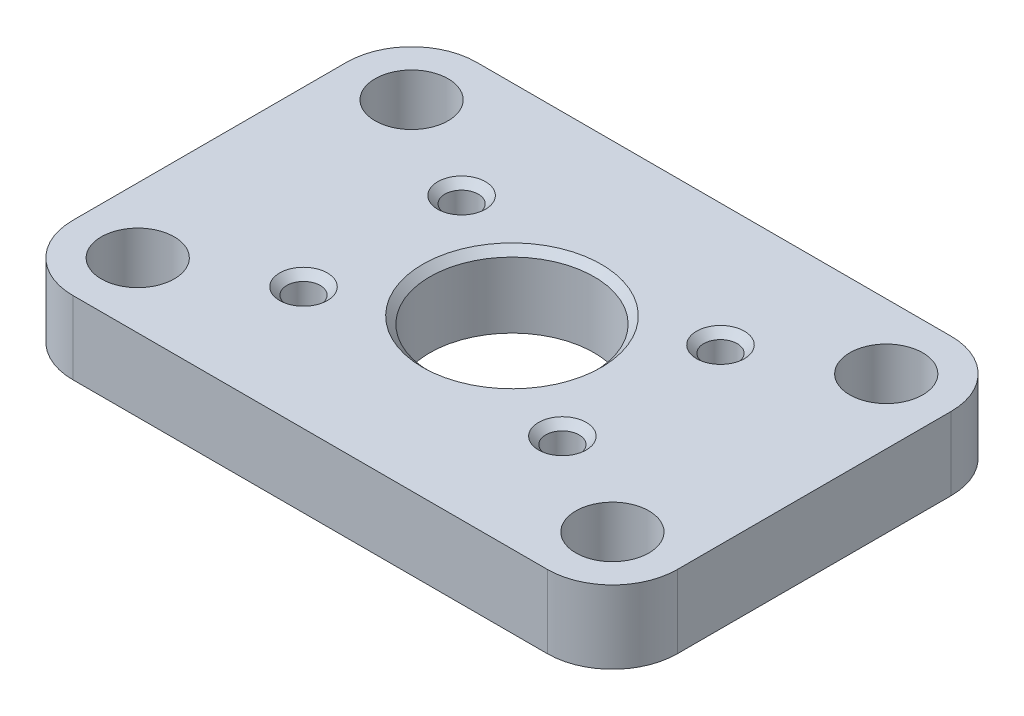
SolidWorks part; units mm, degrees
ref_plane "Front Plane" through (0, 0, 0) normal (0, 0, 1) x (1, 0, 0)
ref_plane "Top Plane" through (0, 0, 0) normal (0, 1, 0) x (1, 0, 0)
ref_plane "Right Plane" through (0, 0, 0) normal (1, 0, 0) x (0, 0, -1)
sketch "Sketch1" plane through (0, 0, 0) normal (0, 1, 0) x (1, 0, 0)
  line L1 (-16.51, -14.0462) -> (16.51, -14.0462)
  line L2 (-21.0312, -9.525) -> (-21.0312, 9.525)
  line L3 (-16.51, 14.0462) -> (16.51, 14.0462)
  line L4 (21.0312, -9.525) -> (21.0312, 9.525)
  line L5 (-21.0312, -14.0462) -> (21.0312, 14.0462) construction
  line L6 (-21.0312, 14.0462) -> (21.0312, -14.0462) construction
  arc A0 (16.51, -14.0462) -> (21.0312, -9.525) centre (16.51, -9.525) ccw
  arc A1 (16.51, 14.0462) -> (21.0312, 9.525) centre (16.51, 9.525) cw
  arc A2 (-16.51, -14.0462) -> (-21.0312, -9.525) centre (-16.51, -9.525) cw
  arc A3 (-21.0312, 9.525) -> (-16.51, 14.0462) centre (-16.51, 9.525) cw
  circle A4 centre (-16.51, 9.525) radius 2.54
  circle A5 centre (-16.51, -9.525) radius 2.54
  circle A6 centre (16.51, -9.525) radius 2.54
  circle A7 centre (16.51, 9.525) radius 2.54
  point P0 (0, 0)
  dimension "D1" = 4.5212
  dimension "D4" = 5.08
  dimension "D2" = 33.02
  dimension "D3" = 19.05
extrude "Boss-Extrude1" add sketch "Sketch1" along normal blind 5.08
sketch "Sketch3" plane through (0, 5.08, 0) normal (0, 1, 0) x (1, 0, 0)
  line L1 (-9.0043, -5.4991) -> (9.0043, -5.4991) construction
  line L2 (-9.0043, -5.4991) -> (-9.0043, 5.4991) construction
  line L3 (-9.0043, 5.4991) -> (9.0043, 5.4991) construction
  line L4 (9.0043, -5.4991) -> (9.0043, 5.4991) construction
  line L5 (-9.0043, -5.4991) -> (9.0043, 5.4991) construction
  line L6 (-9.0043, 5.4991) -> (9.0043, -5.4991) construction
  circle A0 centre (-9.0043, 5.4991) radius 1.162
  circle A1 centre (9.0043, 5.4991) radius 1.162
  circle A2 centre (9.0043, -5.4991) radius 1.162
  circle A3 centre (-9.0043, -5.4991) radius 1.162
  circle A4 centre (0, 0) radius 5.715
  point P0 (0, 0)
  dimension "D1" = 2.3241
  dimension "D4" = 11.43
  dimension "D2" = 10.9982
  dimension "D3" = 18.0086
extrude "Cut-Extrude4" cut sketch "Sketch3" against normal through all
chamfer "Chamfer1" distance 0.5 angle 45 5 edges at (-9.0043, 5.08, 6.6611) (9.0043, 5.08, 6.6611) (9.0043, 5.08, -4.3371) (-9.0043, 5.08, -4.3371) (0, 5.08, 5.715)
